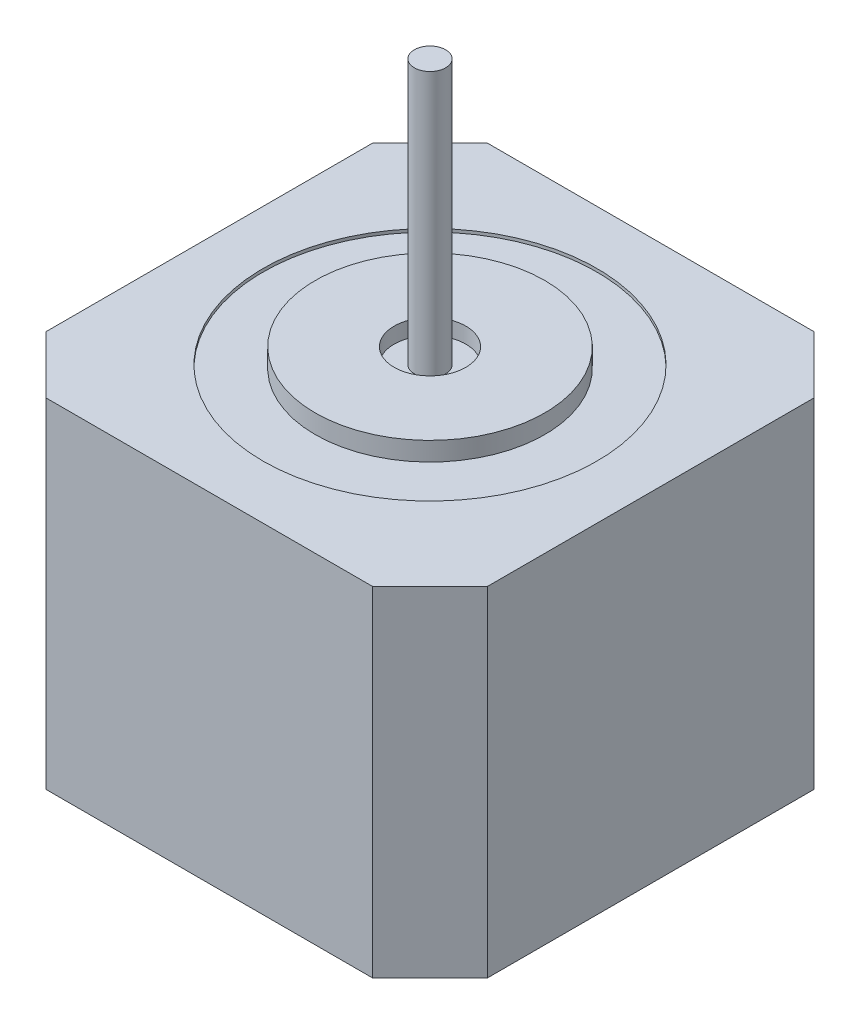
SolidWorks part; units mm, degrees
ref_plane "Front Plane" through (0, 0, 0) normal (0, 0, 1) x (1, 0, 0)
ref_plane "Top Plane" through (0, 0, 0) normal (0, 1, 0) x (1, 0, 0)
ref_plane "Right Plane" through (0, 0, 0) normal (1, 0, 0) x (0, 0, -1)
sketch "Sketch2" plane through (0, 0, 0) normal (0, 1, 0) x (1, 0, 0)
  line L1 (-21.15, -21.15) -> (21.15, -21.15)
  line L2 (-21.15, -21.15) -> (-21.15, 21.15)
  line L3 (-21.15, 21.15) -> (21.15, 21.15)
  line L4 (21.15, -21.15) -> (21.15, 21.15)
  line L5 (-21.15, -21.15) -> (21.15, 21.15) construction
  line L6 (-21.15, 21.15) -> (21.15, -21.15) construction
  point P0 (0, 0)
  dimension "D1" = 42.3
extrude "Boss-Extrude1" add sketch "Sketch2" along normal blind 32.5
chamfer "Chamfer1" distance 5.5 angle 45 4 edges at (-21.15, 16.25, -21.15) (21.15, 16.25, -21.15) (21.15, 16.25, 21.15) (-21.15, 16.25, 21.15)
sketch "Sketch3" plane through (0, 32.5, 0) normal (0, 1, 0) x (1, 0, 0)
  circle A0 centre (0, 0) radius 11
  circle A1 centre (0, 0) radius 3.4309
  dimension "D1" = 22
extrude "Boss-Extrude2" add sketch "Sketch3" along normal blind 1.5
sketch "Sketch4" plane through (0, 32.5, 0) normal (0, 1, 0) x (1, 0, 0)
  circle A0 centre (0, 0) radius 11 construction
  circle A1 centre (0, 0) radius 11
  circle A2 centre (0, 0) radius 16
  dimension "D1" = 5
extrude "Cut-Extrude1" cut sketch "Sketch4" against normal blind 0.3
sketch "Sketch5" plane through (0, 32.5, 0) normal (0, 1, 0) x (1, 0, 0)
  circle A0 centre (0, 0) radius 1.5
  dimension "D1" = 3
extrude "Boss-Extrude3" add sketch "Sketch5" along normal blind 25.4
